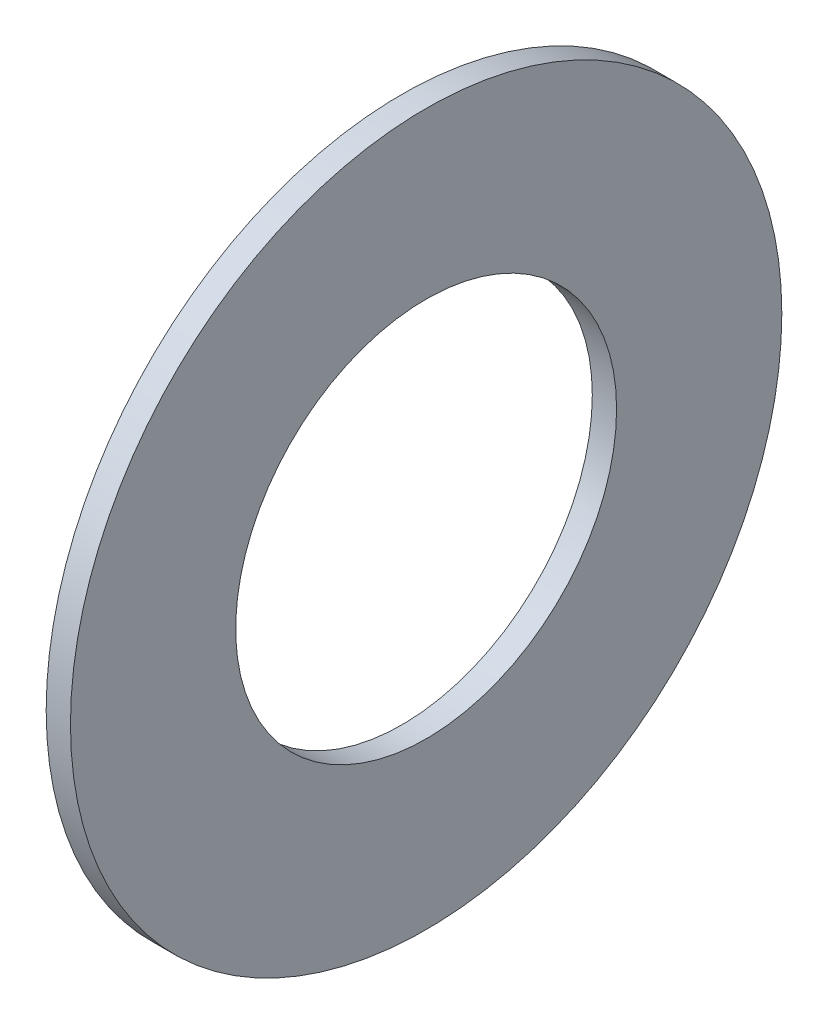
SolidWorks part; units mm, degrees
ref_plane "Front Plane" through (0, 0, 0) normal (0, 0, 1) x (1, 0, 0)
ref_plane "Top Plane" through (0, 0, 0) normal (0, 1, 0) x (1, 0, 0)
ref_plane "Right Plane" through (0, 0, 0) normal (1, 0, 0) x (0, 0, -1)
sketch "Sketch1" plane through (0, 0, 0) normal (1, 0, 0) x (0, 0, -1)
  circle A0 centre (0, 0) radius 11.9062
  circle A1 centre (0, 0) radius 6.3754
  dimension "OD" = 23.8125
  dimension "Shaft Dia" = 12.7508
extrude "Extrude1" add sketch "Sketch1" along normal blind 0.8128
